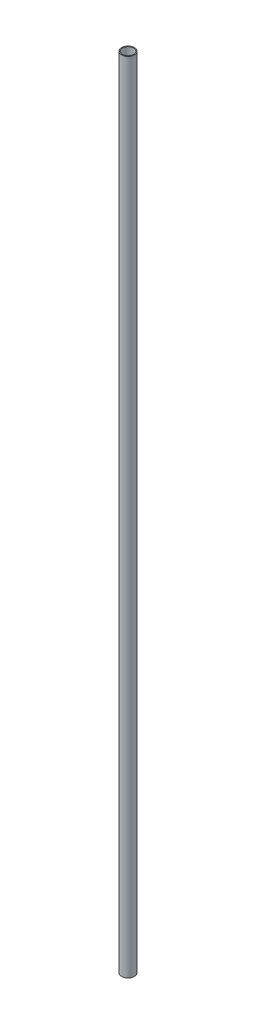
SolidWorks part; units mm, degrees
ref_plane "Front Plane" through (0, 0, 0) normal (0, 0, 1) x (1, 0, 0)
ref_plane "Top Plane" through (0, 0, 0) normal (0, 1, 0) x (1, 0, 0)
ref_plane "Right Plane" through (0, 0, 0) normal (1, 0, 0) x (0, 0, -1)
sketch "Sketch1" plane through (0, 0, 0) normal (0, 1, 0) x (1, 0, 0)
  circle A0 centre (0, 0) radius 4
  circle A1 centre (0, 0) radius 3.5
  dimension "D1" = 8
  dimension "D2" = 7
extrude "Boss-Extrude1" add sketch "Sketch1" along normal blind 500
